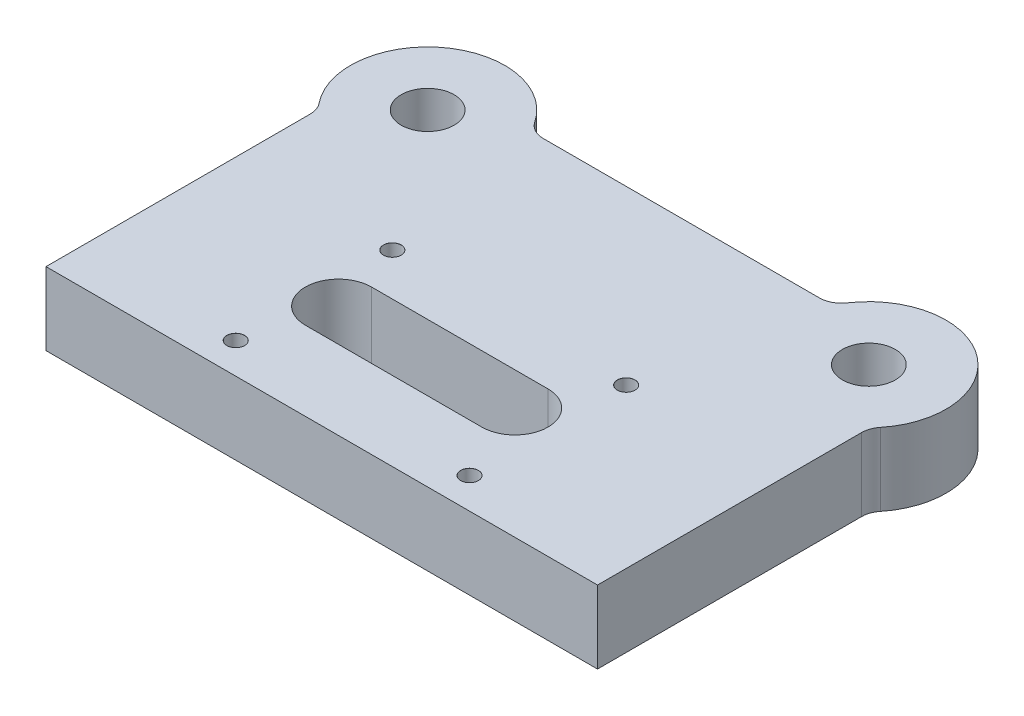
SolidWorks part; units mm, degrees
ref_plane "Front Plane" through (0, 0, 0) normal (0, 0, 1) x (1, 0, 0)
ref_plane "Top Plane" through (0, 0, 0) normal (0, 1, 0) x (1, 0, 0)
ref_plane "Right Plane" through (0, 0, 0) normal (1, 0, 0) x (0, 0, -1)
sketch "Sketch1" plane through (0, 0, 0) normal (0, 1, 0) x (1, 0, 0)
  line L0 (125, 0) -> (-125, 0)
  line L1 (-125, 0) -> (-125, 123.5051)
  line L2 (0, 0) -> (0, 163) construction
  line L3 (68.3772, 163) -> (-68.3772, 163)
  line L4 (125, 0) -> (125, 123.5051)
  arc A0 (-68.3772, 163) -> (-125, 123.5051) centre (-100, 148) ccw
  circle A1 centre (-100, 148) radius 12
  circle A2 centre (100, 148) radius 12
  arc A3 (68.3772, 163) -> (125, 123.5051) centre (100, 148) cw
  dimension "D3" = 70
  dimension "D4" = 24
  dimension "D1" = 250
  dimension "D2" = 148
  dimension "D5" = 163
  dimension "D6" = 200
extrude "Boss-Extrude1" add sketch "Sketch1" along normal blind 33
fillet "Fillet1" radius 10 4 edges at (125, 16.5, -123.5051) (68.3772, 16.5, -163) (-68.3772, 16.5, -163) (-125, 16.5, -123.5051)
hole_wizard "M8 Tapped Hole2" positions "Sketch4" profile "Sketch5" tap size "M8" standard "DIN" end condition up to next
sketch "Sketch4" plane through (0, 33, 0) normal (0, 1, 0) x (1, 0, 0)
  point P0 (-53, 85)
  point P3 (53, 85)
  point P6 (53, 14)
  point P9 (-53, 14)
sketch "Sketch5" plane through (-53, 33, -85) normal (1, 0, 0) x (0, 0, 1)
  line L0 (0, 0) -> (0, 33)
  line L1 (0, 33) -> (4, 33)
  line L2 (4, 33) -> (4, 0.025)
  line L3 (4, 0.025) -> (4.025, 0)
  line L5 (4.025, 0) -> (0, 0)
  line L6 (-4, 0.025) -> (-4.025, 0) construction
  line L11 (0, -6.35) -> (0, 107.95) construction
  dimension "Thread Major Dia." = 8
  dimension "Thru Tap Drill Depth" = 33
  dimension "Near C'Sink Dia." = 8.05
  dimension "Near C'Sink Angle" = 90
sketch "Sketch6" plane through (0, 33, 0) normal (0, 1, 0) x (1, 0, 0)
  line L0 (-43.2169, 50.7721) -> (36.7831, 50.7721) construction
  line L1 (-43.2169, 65.7721) -> (36.7831, 65.7721)
  line L2 (-43.2169, 35.7721) -> (36.7831, 35.7721)
  circle A0 centre (-40.5, 49.5) radius 3 construction
  arc A1 (-43.2169, 65.7721) -> (-43.2169, 35.7721) centre (-43.2169, 50.7721) ccw
  arc A2 (36.7831, 35.7721) -> (36.7831, 65.7721) centre (36.7831, 50.7721) ccw
  point P4 (-3.2169, 50.7721)
  point P9 (0, 0)
  point P10 (0, 0)
  dimension "D2" = 15
  dimension "D1" = 80
extrude "Cut-Extrude1" cut sketch "Sketch6" against normal up to next
